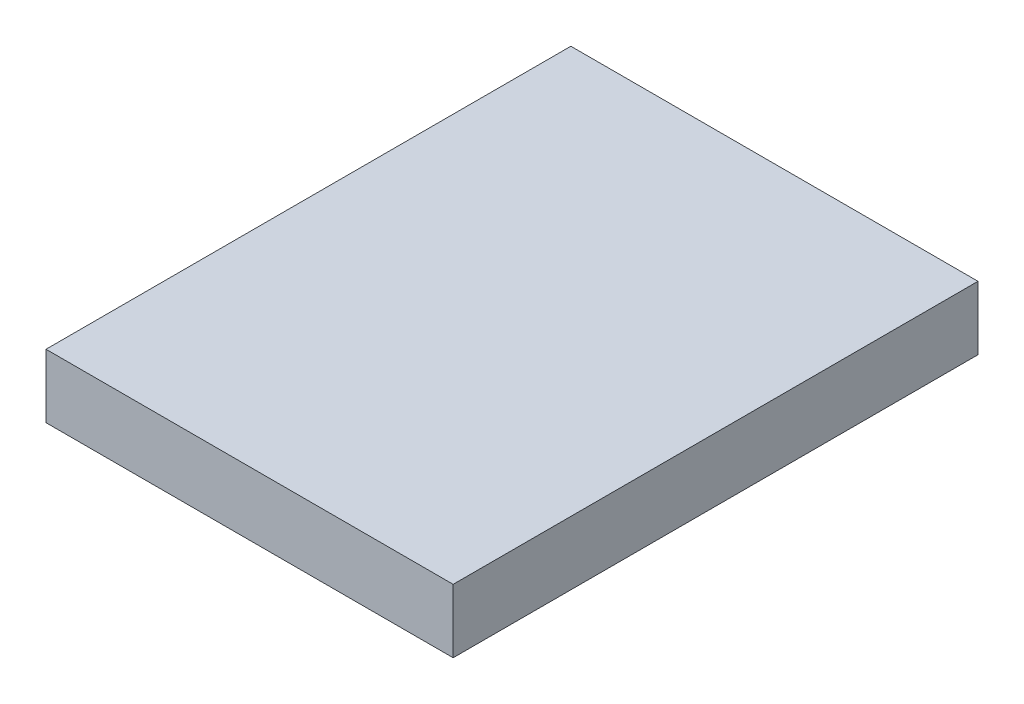
SolidWorks part; units mm, degrees
material "Copper"
ref_plane "Front Plane" through (0, 0, 0) normal (0, 0, 1) x (1, 0, 0)
ref_plane "Top Plane" through (0, 0, 0) normal (0, 1, 0) x (1, 0, 0)
ref_plane "Right Plane" through (0, 0, 0) normal (1, 0, 0) x (0, 0, -1)
sketch "Sketch1" plane through (0, 0, 0) normal (0, 1, 0) x (1, 0, 0)
  line L1 (-17.2667, 7.7911) -> (15.2453, 7.7911)
  line L2 (-17.2667, 7.7911) -> (-17.2667, -34.1189)
  line L3 (-17.2667, -34.1189) -> (15.2453, -34.1189)
  line L4 (15.2453, 7.7911) -> (15.2453, -34.1189)
  dimension "D1" = 32.512
  dimension "D2" = 41.91
extrude "Boss-Extrude1" add sketch "Sketch1" along normal blind 5.08
hole_wizard "Tap Drill for #4-48 Tap1" positions "Sketch2" profile "Sketch3" hole size "#4-48" standard "ANSI Inch"
sketch "Sketch2" plane through (0, 0, -7.7911) normal (0, 0, -1) x (-1, 0, 0)
  line L0 (17.2667, 5.08) -> (17.2667, 0) construction
  point P0 (12.1867, 2.7184)
  point P2 (-10.6733, 2.7184)
  dimension "D1" = 5.08
  dimension "D2" = 22.86
sketch "Sketch3" plane through (-12.1867, 2.7184, -7.7911) normal (1, 0, 0) x (0, 1, 0)
  line L0 (0, 0) -> (0, 10.8735)
  line L1 (0, 10.8735) -> (1.1874, 10.16)
  line L2 (1.1874, 10.16) -> (1.1874, 0)
  line L5 (1.1874, 0) -> (0, 0)
  line L10 (0, 10.8735) -> (-1.1874, 10.16) construction
  line L11 (0, -6.35) -> (0, 107.95) construction
  dimension "Hole Dia." = 2.3749
  dimension "Hole Depth" = 10.16
  dimension "Drill Angle" = 118
